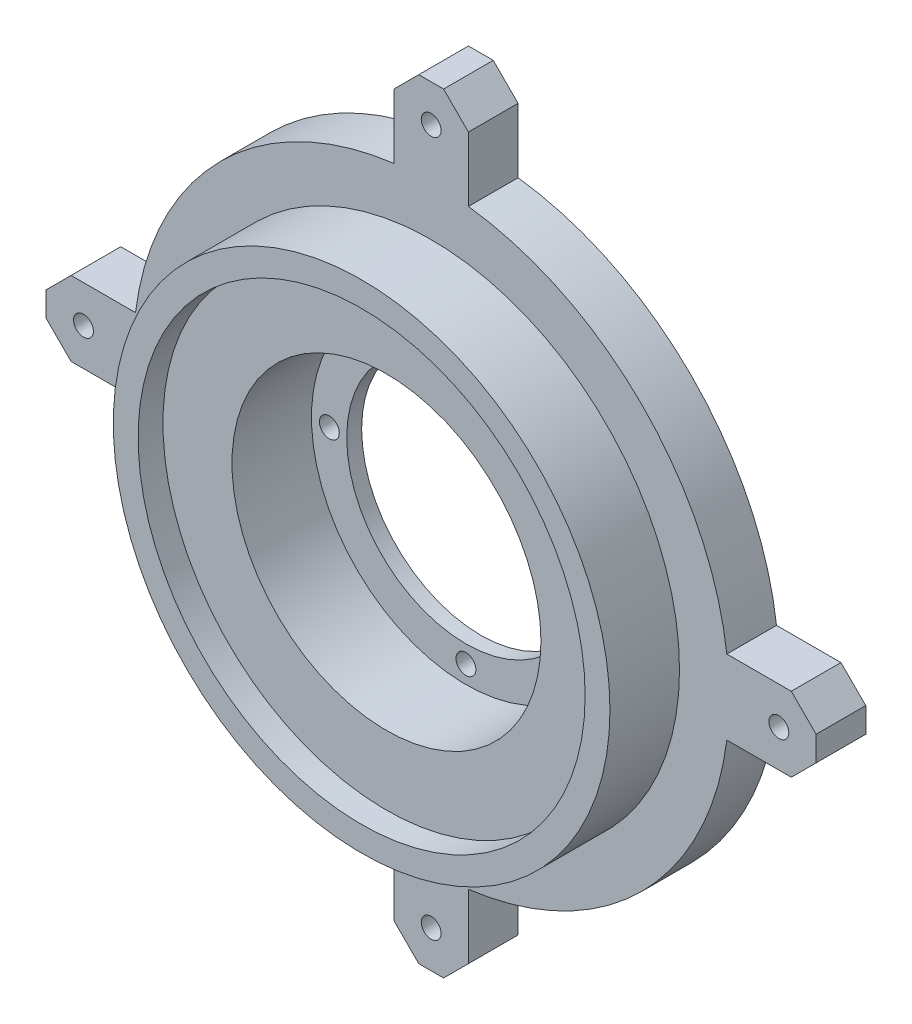
SolidWorks part; units mm, degrees
ref_plane "Front Plane" through (0, 0, 0) normal (0, 0, 1) x (1, 0, 0)
ref_plane "Top Plane" through (0, 0, 0) normal (0, 1, 0) x (1, 0, 0)
ref_plane "Right Plane" through (0, 0, 0) normal (1, 0, 0) x (0, 0, -1)
sketch "Sketch1" plane through (0, 0, 0) normal (0, 0, 1) x (1, 0, 0)
  line L0 (-72.5, 7.5) -> (-77.5, 2.5)
  line L1 (-42.5, -7.5) -> (-72.5, -7.5)
  line L2 (-42.5, -7.5) -> (-42.5, 7.5)
  line L3 (-42.5, 7.5) -> (-72.5, 7.5)
  line L4 (-77.5, -2.5) -> (-77.5, 2.5)
  line L5 (-42.5, -7.5) -> (-77.5, 7.5) construction
  line L6 (-42.5, 7.5) -> (-77.5, -7.5) construction
  line L7 (-72.5, -7.5) -> (-77.5, -2.5)
  line L8 (-7.5, 42.5) -> (7.5, 42.5)
  line L9 (-7.5, 42.5) -> (-7.5, 72.5)
  line L10 (-7.5, 72.5) -> (-2.5, 77.5)
  line L11 (-2.5, 77.5) -> (2.5, 77.5)
  line L12 (7.5, 72.5) -> (2.5, 77.5)
  line L13 (7.5, 42.5) -> (7.5, 72.5)
  line L14 (42.5, 7.5) -> (42.5, -7.5)
  line L15 (42.5, 7.5) -> (72.5, 7.5)
  line L16 (72.5, 7.5) -> (77.5, 2.5)
  line L17 (77.5, 2.5) -> (77.5, -2.5)
  line L18 (72.5, -7.5) -> (77.5, -2.5)
  line L19 (42.5, -7.5) -> (72.5, -7.5)
  line L20 (7.5, -42.5) -> (-7.5, -42.5)
  line L21 (7.5, -42.5) -> (7.5, -72.5)
  line L22 (7.5, -72.5) -> (2.5, -77.5)
  line L23 (2.5, -77.5) -> (-2.5, -77.5)
  line L24 (-7.5, -72.5) -> (-2.5, -77.5)
  line L25 (-7.5, -42.5) -> (-7.5, -72.5)
  circle A0 centre (0, 0) radius 60
  point P3 (-60, 0)
  point P33 (0, 0)
  dimension "D1" = 120
  dimension "D2" = 35
  dimension "D3" = 15
  dimension "D4" = 4
extrude "Boss-Extrude1" add sketch "Sketch1" along normal blind 10 contours L3 A0 L1 L2 | L15 A0 L13 L8 L9 L3 L2 L1 L25 L20 L21 L19 L14 | L13 A0 L9 L8 | A0 L13 L12 L11 L10 L9 | A0 L3 L0 L4 L7 L1 | L19 A0 L15 L14 | A0 L19 L18 L17 L16 L15 | A0 L25 L24 L23 L22 L21 | L25 A0 L21 L20
sketch "Sketch2" plane through (0, 0, 10) normal (0, 0, 1) x (1, 0, 0)
  circle A0 centre (0, 0) radius 50
  dimension "D1" = 100
extrude "Boss-Extrude2" add sketch "Sketch2" along normal blind 14
sketch "Sketch3" plane through (0, 0, 24) normal (0, 0, 1) x (1, 0, 0)
  circle A0 centre (0, 0) radius 31.1
  dimension "D1" = 62.2
extrude "Cut-Extrude1" cut sketch "Sketch3" against normal blind 21
sketch "Sketch4" plane through (0, 0, 0) normal (0, 0, -1) x (-1, 0, 0)
  circle A2 centre (0, 0) radius 24
  dimension "D1" = 48
hole_wizard "Ø4.0mm Dowel Hole1" positions "Sketch10" profile "Sketch6" hole size "Ø4.0" standard "ANSI Metric" end condition through all
sketch "Sketch10" plane through (0, 0, 0) normal (0, 0, -1) x (-1, 0, 0)
  point P4 (-70, 0)
  point P10 (0, 70)
  point P11 (70, 0)
  point P12 (0, -70)
  dimension "D2" = 70
  dimension "D1" = 4
sketch "Sketch6" plane through (70, 0, 0) normal (1, 0, 0) x (0, 1, 0)
  line L0 (0, 0) -> (0, 24)
  line L1 (0, 24) -> (2, 24)
  line L2 (2, 24) -> (2, 0.025)
  line L3 (2, 0.025) -> (2.025, 0)
  line L5 (2.025, 0) -> (0, 0)
  line L6 (-2, 0.025) -> (-2.025, 0) construction
  line L11 (0, -6.35) -> (0, 107.95) construction
  dimension "Thru Hole Dia." = 4
  dimension "Thru Hole Depth" = 24
  dimension "Near C'Sink Dia." = 4.05
  dimension "Near C'Sink Angle" = 90
sketch "Sketch11" plane through (0, 0, 24) normal (0, 0, 1) x (1, 0, 0)
  circle A0 centre (0, 0) radius 45
  dimension "D1" = 90
extrude "Cut-Extrude2" cut sketch "Sketch11" against normal blind 5
extrude "Cut-Extrude3" cut sketch "Sketch4" against normal blind 4
sketch "Sketch12" plane through (0, 0, 0) normal (0, 0, -1) x (-1, 0, 0)
  circle A0 centre (27.5, 0) radius 2
  circle A1 centre (0, -27.5) radius 2
  circle A2 centre (-27.5, 0) radius 2
  circle A3 centre (0, 27.5) radius 2
  point P12 (0, 0)
  dimension "D1" = 27.5
  dimension "D2" = 4
extrude "Cut-Extrude5" cut sketch "Sketch12" against normal blind 4
